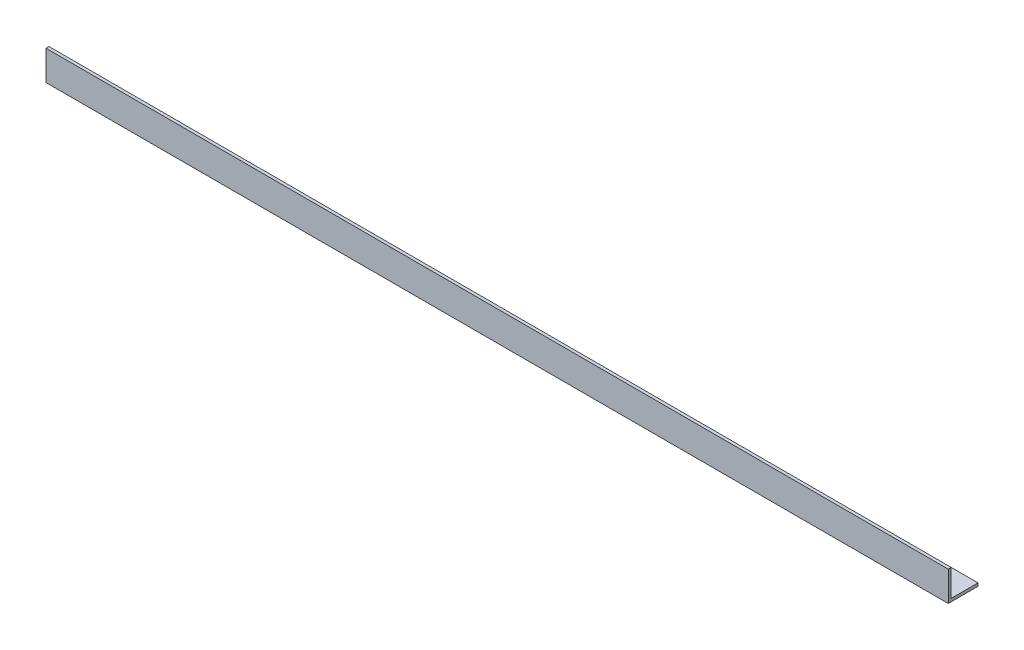
SolidWorks part; units mm, degrees
ref_plane "Спереди" through (0, 0, 0) normal (0, 0, 1) x (1, 0, 0)
ref_plane "Сверху" through (0, 0, 0) normal (0, 1, 0) x (1, 0, 0)
ref_plane "Справа" through (0, 0, 0) normal (1, 0, 0) x (0, 0, -1)
sketch "Эскиз1" plane through (0, 0, 0) normal (1, 0, 0) x (0, 0, -1)
  line L0 (0, 0) -> (0, 15)
  line L1 (0, 15) -> (1.5, 15)
  line L2 (1.5, 15) -> (1.5, 1.5)
  line L3 (1.5, 1.5) -> (15, 1.5)
  line L4 (15, 1.5) -> (15, 0)
  line L5 (15, 0) -> (0, 0)
  dimension "D1" = 15
  dimension "D2" = 15
  dimension "D3" = 1.5
  dimension "D4" = 1.5
extrude "Бобышка-Вытянуть1" add sketch "Эскиз1" along normal blind 455
